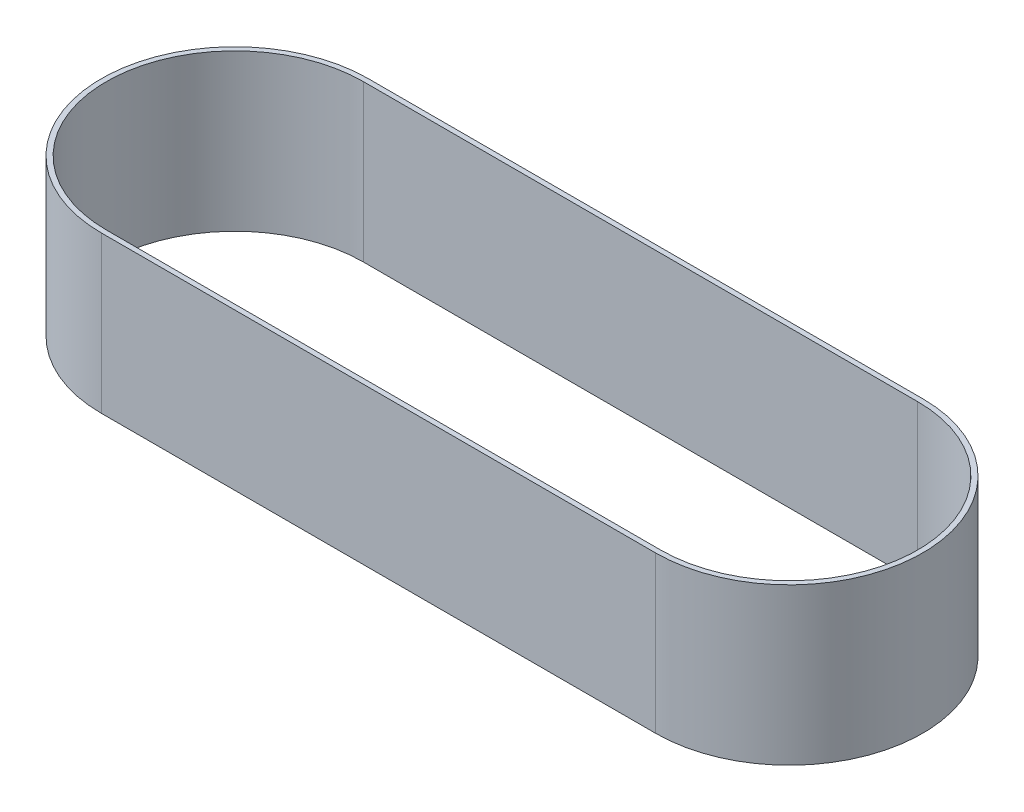
SolidWorks part; units mm, degrees
ref_plane "Front Plane" through (0, 0, 0) normal (0, 0, 1) x (1, 0, 0)
ref_plane "Top Plane" through (0, 0, 0) normal (0, 1, 0) x (1, 0, 0)
ref_plane "Right Plane" through (0, 0, 0) normal (1, 0, 0) x (0, 0, -1)
sketch "Sketch1" plane through (0, 0, 0) normal (0, 1, 0) x (1, 0, 0)
  line L0 (-110, 51) -> (110, 51)
  line L1 (-110, -53) -> (110, -53)
  line L3 (-110, 53) -> (110, 53)
  line L5 (-110, -53) -> (110, 53) construction
  line L6 (-110, 53) -> (110, -53) construction
  line L7 (-110, -51) -> (110, -51)
  arc A0 (-110, 53) -> (-110, -53) centre (-110, 0) ccw
  arc A1 (110, -53) -> (110, 53) centre (110, 0) ccw
  arc A2 (110, -51) -> (110, 51) centre (110, 0) ccw
  arc A3 (-110, 51) -> (-110, -51) centre (-110, 0) ccw
  point P0 (0, 0)
  dimension "D1" = 220
  dimension "D2" = 106
  dimension "D3" = 2
extrude "Boss-Extrude1" add sketch "Sketch1" along normal blind 62
